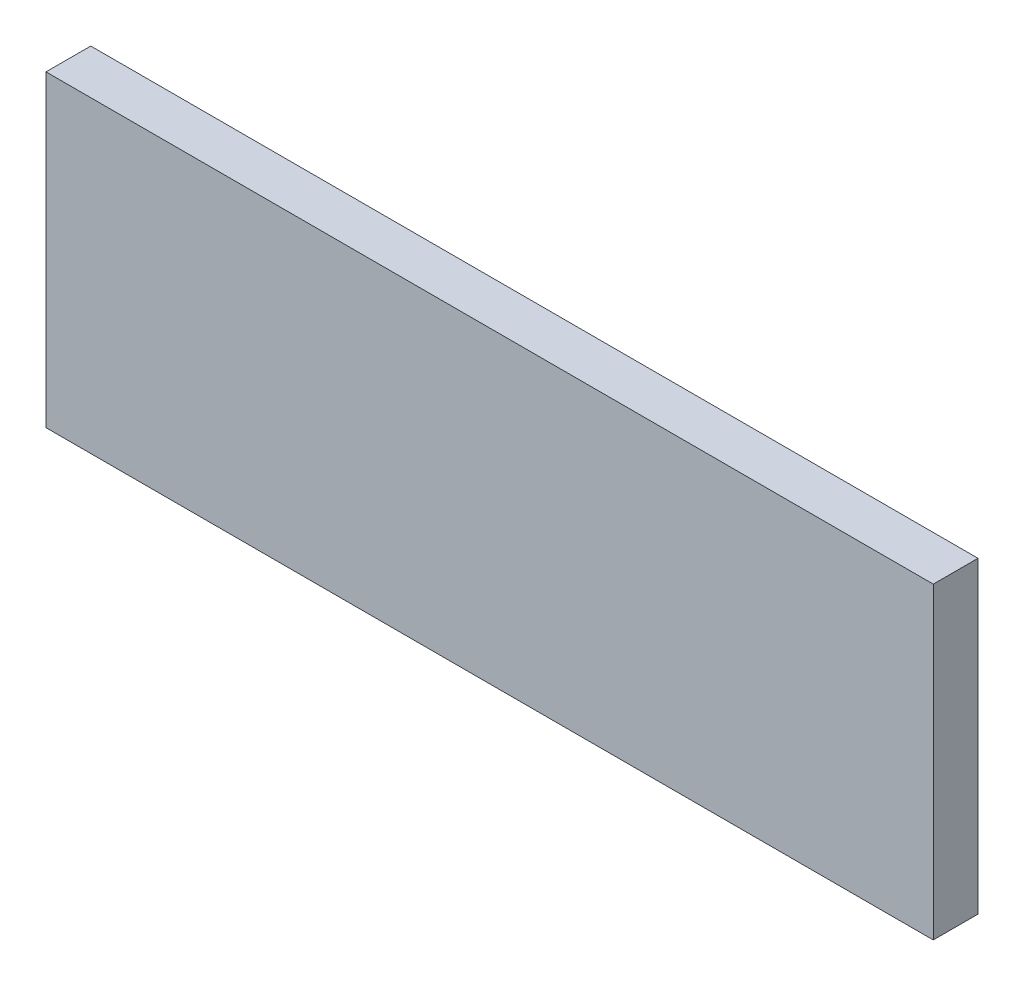
SolidWorks part; units mm, degrees
ref_plane "Спереди" through (0, 0, 0) normal (0, 0, 1) x (1, 0, 0)
ref_plane "Сверху" through (0, 0, 0) normal (0, 1, 0) x (1, 0, 0)
ref_plane "Справа" through (0, 0, 0) normal (1, 0, 0) x (0, 0, -1)
sketch "Эскиз1" plane through (0, 0, 0) normal (0, 0, 1) x (1, 0, 0)
  line L1 (339.265, -116.3993) -> (-17.735, -116.3993)
  line L2 (339.265, -116.3993) -> (339.265, 7.6007)
  line L3 (339.265, 7.6007) -> (-17.735, 7.6007)
  line L4 (-17.735, -116.3993) -> (-17.735, 7.6007)
  dimension "D1" = 357
  dimension "D2" = 124
extrude "Бобышка-Вытянуть1" add sketch "Эскиз1" along normal blind 18
